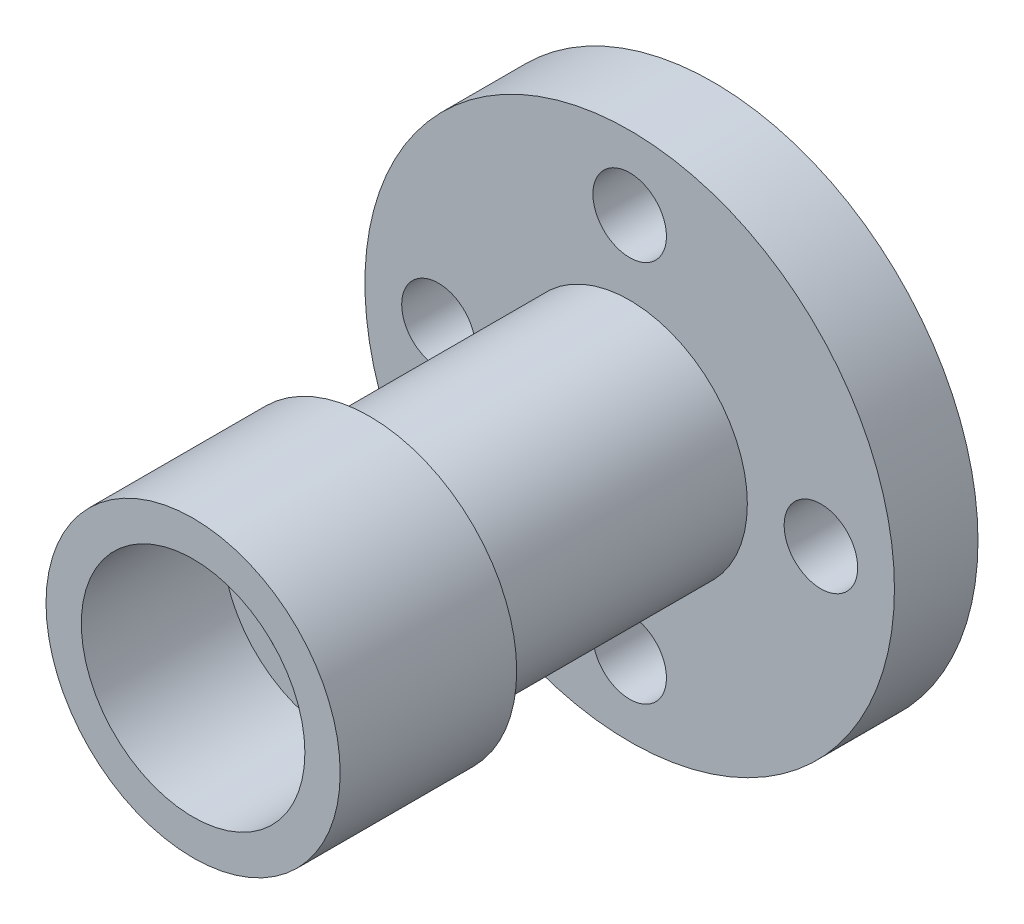
SolidWorks part; units mm, degrees
ref_plane "Alzado" through (0, 0, 0) normal (0, 0, 1) x (1, 0, 0)
ref_plane "Planta" through (0, 0, 0) normal (0, 1, 0) x (1, 0, 0)
ref_plane "Vista lateral" through (0, 0, 0) normal (1, 0, 0) x (0, 0, -1)
sketch "Croquis1" plane through (0, 0, 0) normal (0, 0, 1) x (1, 0, 0)
  circle A0 centre (0, 0) radius 45
  dimension "D1" = 90
extrude "Saliente-Extruir1" add sketch "Croquis1" along normal blind 14.2
ref_plane "Plano2" through (0, 0, 14.2) normal (0, 0, 1) x (1, 0, 0)
sketch "Croquis2" plane through (0, 0, 14.2) normal (0, 0, 1) x (1, 0, 0)
  circle A0 centre (0, 0) radius 20
  dimension "D1" = 40
extrude "Saliente-Extruir2" add sketch "Croquis2" along normal blind 44.2
ref_plane "Plano3" through (0, 0, 58.4) normal (0, 0, 1) x (1, 0, 0)
sketch "Croquis3" plane through (0, 0, 58.4) normal (0, 0, 1) x (1, 0, 0)
  circle A0 centre (0, 0) radius 25
  dimension "D1" = 50
extrude "Saliente-Extruir3" add sketch "Croquis3" along normal blind 30 contours A0
ref_plane "Plano4" through (0, 0, 88.4) normal (0, 0, 1) x (1, 0, 0)
sketch "Croquis4" plane through (0, 0, 88.4) normal (0, 0, 1) x (1, 0, 0)
  circle A0 centre (0, 0) radius 19
  dimension "D1" = 38
extrude "Cortar-Extruir1" cut sketch "Croquis4" against normal blind 24 contours A0
ref_plane "Plano5" through (0, 0, 64.4) normal (0, 0, 1) x (1, 0, 0)
sketch "Croquis5" plane through (0, 0, 64.4) normal (0, 0, 1) x (1, 0, 0)
  circle A0 centre (0, 0) radius 15
  dimension "D1" = 30
extrude "Cortar-Extruir2" cut sketch "Croquis5" against normal blind 84
chamfer "Chaflán1" distance 3.5 distance2 3 1 edges at (15, 0, 0)
sketch "Croquis6" plane through (0, 0, 0) normal (0, 0, -1) x (-1, 0, 0)
  line L0 (0, 0) -> (0, 32.5) construction
  circle A0 centre (0, 32.5) radius 6.25
  circle A1 centre (32.5, 0) radius 6.25
  circle A2 centre (0, -32.5) radius 6.25
  circle A3 centre (-32.5, 0) radius 6.25
  point P13 (0, 0)
  dimension "D2" = 12.5
  dimension "D1" = 32.5
  dimension "D3" = 4
extrude "Cortar-Extruir3" cut sketch "Croquis6" against normal blind 84
